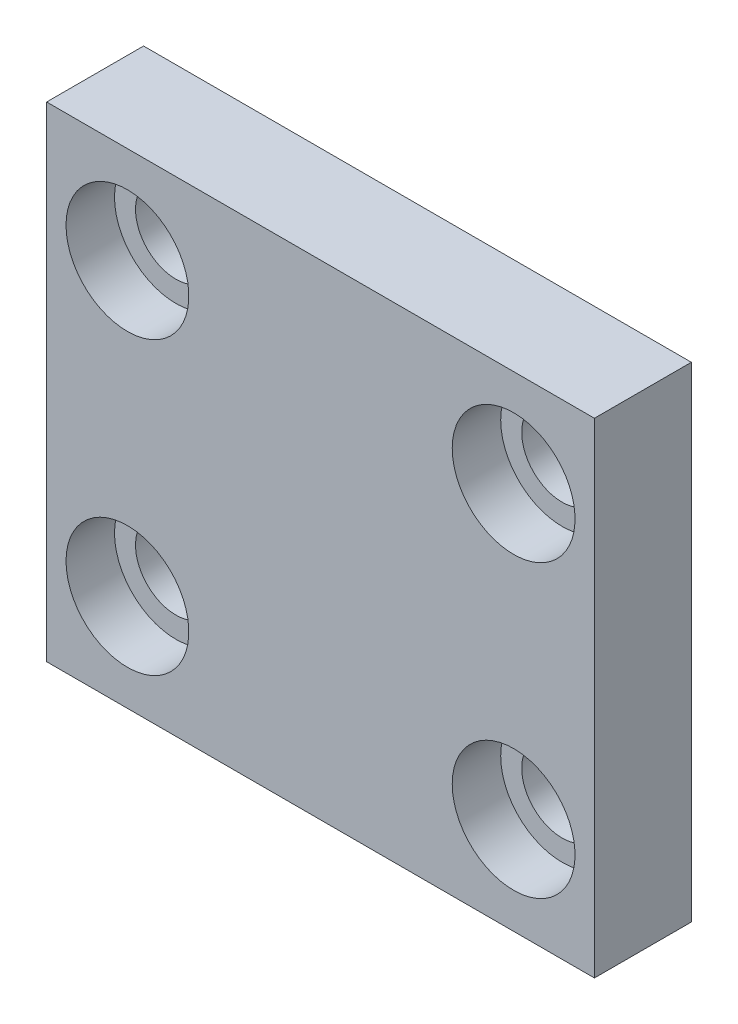
SolidWorks part; units mm, degrees
ref_plane "Front Plane" through (0, 0, 0) normal (0, 0, 1) x (1, 0, 0)
ref_plane "Top Plane" through (0, 0, 0) normal (0, 1, 0) x (1, 0, 0)
ref_plane "Right Plane" through (0, 0, 0) normal (1, 0, 0) x (0, 0, -1)
sketch "Sketch1" plane through (0, 0, 0) normal (0, 0, 1) x (1, 0, 0)
  line L1 (-16.95, -15) -> (16.95, -15)
  line L2 (-16.95, -15) -> (-16.95, 15)
  line L3 (-16.95, 15) -> (16.95, 15)
  line L4 (16.95, -15) -> (16.95, 15)
  line L5 (-16.95, -15) -> (16.95, 15) construction
  line L6 (-16.95, 15) -> (16.95, -15) construction
  point P0 (0, 0)
  dimension "D1" = 33.9
  dimension "D2" = 30
extrude "Boss-Extrude5" add sketch "Sketch1" along normal blind 3
sketch "Sketch3" plane through (0, 0, 3) normal (0, 0, 1) x (1, 0, 0)
  line L0 (16.95, 15) -> (-16.95, 15) construction
  line L1 (-16.95, 15) -> (-16.95, -15) construction
  line L2 (16.95, -15) -> (16.95, 15) construction
  line L3 (-16.95, -15) -> (16.95, -15) construction
  circle A0 centre (-11.95, 9) radius 2.5
  circle A1 centre (11.95, 9) radius 2.5
  circle A2 centre (11.95, -9) radius 2.5
  circle A3 centre (-11.95, -9) radius 2.5
  dimension "D1" = 5
  dimension "D2" = 6
  dimension "D3" = 5
  dimension "D4" = 6
  dimension "D5" = 5
  dimension "D6" = 5
  dimension "D7" = 6
  dimension "D8" = 5
  dimension "D9" = 5
  dimension "D10" = 6
  dimension "D11" = 5
  dimension "D12" = 5
extrude "Cut-Extrude2" cut sketch "Sketch3" against normal blind 3
sketch "Sketch7" plane through (0, 0, 3) normal (0, 0, 1) x (1, 0, 0)
  line L1 (-16.95, -15) -> (16.95, -15)
  line L2 (-16.95, -15) -> (-16.95, 15)
  line L3 (-16.95, 15) -> (16.95, 15)
  line L4 (16.95, -15) -> (16.95, 15)
  line L5 (-16.95, -15) -> (16.95, 15) construction
  line L6 (-16.95, 15) -> (16.95, -15) construction
  point P0 (0, 0)
extrude "Boss-Extrude6" add sketch "Sketch7" along normal blind 3
sketch "Sketch8" plane through (0, 0, 3) normal (0, 0, -1) x (-1, 0, 0)
  circle A0 centre (11.95, 9) radius 3.8
  dimension "D1" = 7.6
extrude "Cut-Extrude3" cut sketch "Sketch8" against normal blind 3
sketch "Sketch10" plane through (0, 0, 3) normal (0, 0, -1) x (-1, 0, 0)
  circle A0 centre (-11.95, 9) radius 3.8
  circle A1 centre (-11.95, -9) radius 3.8
  circle A2 centre (11.95, -9) radius 3.8
  dimension "D1" = 7.6
  dimension "D2" = 7.6
  dimension "D3" = 7.6
extrude "Cut-Extrude4" cut sketch "Sketch10" against normal blind 3
